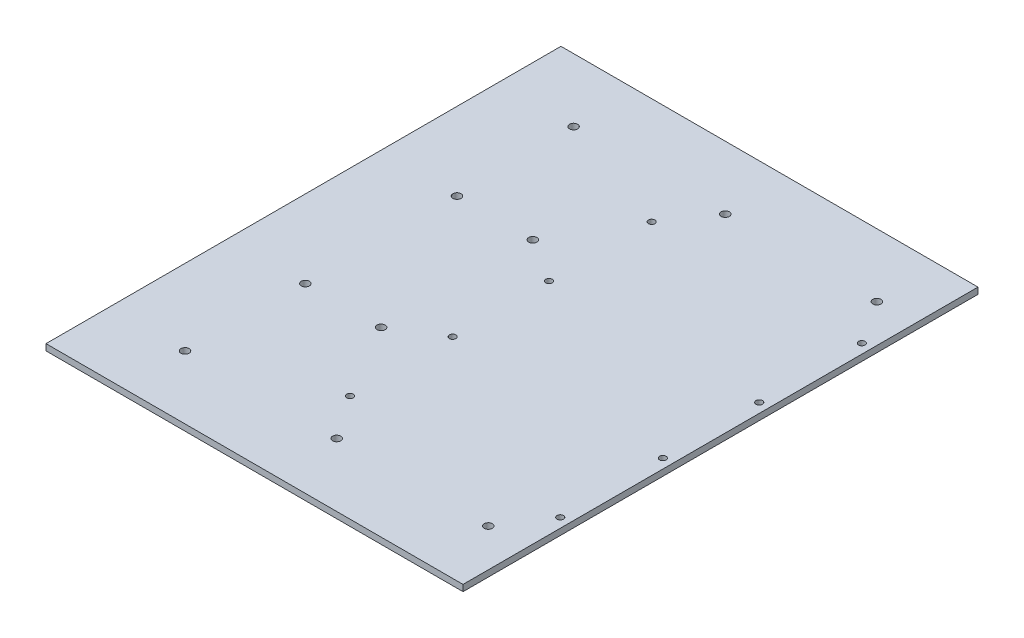
SolidWorks part; units mm, degrees
ref_plane "Front Plane" through (0, 0, 0) normal (0, 0, 1) x (1, 0, 0)
ref_plane "Top Plane" through (0, 0, 0) normal (0, 1, 0) x (1, 0, 0)
ref_plane "Right Plane" through (0, 0, 0) normal (1, 0, 0) x (0, 0, -1)
sketch "Sketch1" plane through (0, 0, 0) normal (0, 1, 0) x (1, 0, 0)
  line L0 (-116.1676, -258.7625) -> (302.9324, 258.7625) construction
  line L1 (-116.1676, -258.7625) -> (302.9324, -258.7625)
  line L2 (-116.1676, -258.7625) -> (-116.1676, 258.7625)
  line L3 (-116.1676, 258.7625) -> (302.9324, 258.7625)
  line L4 (302.9324, -258.7625) -> (302.9324, 258.7625)
  line L5 (-116.1676, 258.7625) -> (302.9324, -258.7625) construction
  point P0 (0, 0)
  point P6 (93.3824, 0)
  point P8 (93.3824, 0)
  dimension "D1" = 517.525
  dimension "D2" = 419.1
extrude "Boss-Extrude1" add sketch "Sketch1" against normal blind 6.35
sketch "Sketch2" plane through (0, 0, 0) normal (0, 1, 0) x (1, 0, 0)
  line L0 (-116.1676, 0) -> (302.9324, 0) construction
  line L1 (-116.1676, 258.7625) -> (-116.1676, -258.7625) construction
  line L2 (302.9324, -258.7625) -> (302.9324, 258.7625) construction
  line L3 (82.1429, -258.7625) -> (82.1429, 258.7625) construction
  line L4 (264.8324, -258.7625) -> (264.8324, 258.7625) construction
  line L5 (-116.1676, 195.2625) -> (302.9324, 195.2625) construction
  line L6 (-116.1676, -195.2625) -> (302.9324, -195.2625) construction
  line L7 (293.4074, 258.7625) -> (293.4074, -258.7625) construction
  line L8 (302.9324, 258.7625) -> (-116.1676, 258.7625) construction
  line L9 (25.4, -38.1) -> (-25.4, -38.1)
  line L10 (25.4, -38.1) -> (25.4, 38.1)
  line L11 (25.4, 38.1) -> (-25.4, 38.1)
  line L12 (-25.4, -38.1) -> (-25.4, 38.1)
  line L13 (25.4, -38.1) -> (-25.4, 38.1) construction
  line L14 (25.4, 38.1) -> (-25.4, -38.1) construction
  line L15 (-116.1676, -258.7625) -> (302.9324, -258.7625) construction
  point P12 (0, 0)
  point P14 (293.4074, 48.438)
  point P20 (293.4074, 151.562)
  point P22 (82.1429, 48.438)
  point P23 (82.1429, 151.562)
  point P26 (82.1429, -151.562)
  point P27 (82.1429, -48.438)
  point P28 (293.4074, -151.562)
  point P29 (293.4074, -48.438)
  dimension "D1" = 76.2
  dimension "D2" = 50.8
  dimension "D3" = 9.525
  dimension "D4" = 211.2645
  dimension "D5" = 38.1
  dimension "D6" = 63.5
hole_wizard "F (0.257) Diameter Hole1" positions "Sketch3" profile "Sketch4" hole size "F" standard "ANSI Inch" end condition up to next
sketch "Sketch3" plane through (0, 0, 0) normal (0, 1, 0) x (1, 0, 0)
  point P0 (82.1429, -151.562)
  point P3 (293.4074, -151.562)
  point P6 (82.1429, -48.438)
  point P9 (293.4074, -48.438)
  point P12 (293.4074, 48.438)
  point P15 (82.1429, 48.438)
  point P18 (82.1429, 151.562)
  point P21 (293.4074, 151.562)
sketch "Sketch4" plane through (82.1429, 0, 151.562) normal (1, 0, 0) x (0, 0, 1)
  line L0 (0, 0) -> (0, 6.35)
  line L1 (0, 6.35) -> (3.2639, 6.35)
  line L2 (3.2639, 6.35) -> (3.2639, 0)
  line L5 (3.2639, 0) -> (0, 0)
  line L11 (0, -6.35) -> (0, 107.95) construction
  dimension "Thru Hole Dia." = 6.5278
  dimension "Thru Hole Depth" = 6.35
sketch "Sketch5" plane through (0, 0, 0) normal (0, 1, 0) x (1, 0, 0)
  line L0 (-116.1676, 258.7625) -> (-116.1676, -258.7625) construction
  line L2 (-116.1676, 233.3625) -> (-116.1676, 258.7625)
  line L3 (302.9324, 0) -> (-116.1676, 0) construction
  line L4 (82.1429, 258.7625) -> (-116.1676, 258.7625)
  line L5 (82.1429, 233.3625) -> (-116.1676, 233.3625)
  line L6 (82.1429, 233.3625) -> (82.1429, 258.7625)
  line L7 (82.1429, -233.3625) -> (-116.1676, -233.3625)
  line L8 (82.1429, -233.3625) -> (82.1429, -258.7625)
  line L9 (82.1429, -258.7625) -> (-116.1676, -258.7625)
  line L10 (-116.1676, -233.3625) -> (-116.1676, -258.7625)
  dimension "D3" = 25.4
  dimension "D4" = 198.3105
extrude "Cut-Extrude1" [suppressed] cut sketch "Sketch5" against normal through all
sketch "Sketch6" plane through (0, 0, 0) normal (0, 1, 0) x (1, 0, 0)
  line L1 (38.1, -76.2) -> (-38.1, -76.2)
  line L2 (38.1, -76.2) -> (38.1, 76.2)
  line L3 (38.1, 76.2) -> (-38.1, 76.2)
  line L4 (-38.1, -76.2) -> (-38.1, 76.2)
  line L5 (38.1, -76.2) -> (-38.1, 76.2) construction
  line L6 (38.1, 76.2) -> (-38.1, -76.2) construction
  point P0 (0, 0)
  dimension "D1" = 76.2
  dimension "D2" = 152.4
hole_wizard "P (0.323) Diameter Hole1" positions "Sketch7" profile "Sketch8" hole size "P" standard "ANSI Inch" end condition through all
sketch "Sketch7" plane through (0, 0, 0) normal (0, 1, 0) x (1, 0, 0)
  point P0 (-38.1, -76.2)
  point P3 (38.1, -76.2)
  point P6 (38.1, 76.2)
  point P9 (-38.1, 76.2)
sketch "Sketch8" plane through (-38.1, 0, 76.2) normal (1, 0, 0) x (0, 0, 1)
  line L0 (0, 0) -> (0, 6.35)
  line L1 (0, 6.35) -> (4.1021, 6.35)
  line L2 (4.1021, 6.35) -> (4.1021, 0)
  line L5 (4.1021, 0) -> (0, 0)
  line L11 (0, -6.35) -> (0, 107.95) construction
  dimension "Thru Hole Dia." = 8.2042
  dimension "Thru Hole Depth" = 6.35
sketch "Sketch9" plane through (0, 0, 0) normal (0, 1, 0) x (1, 0, 0)
  line L0 (302.9324, -258.7625) -> (302.9324, 258.7625) construction
  line L2 (-116.1676, -258.7625) -> (302.9324, -258.7625) construction
  circle A0 centre (264.8324, -195.2625) radius 4.1021
  circle A1 centre (112.4324, -195.2625) radius 4.1021
  circle A2 centre (-39.9676, -195.2625) radius 4.1021
  circle A3 centre (112.4324, 195.2625) radius 4.1021
  circle A4 centre (-39.9676, 195.2625) radius 4.1021
  circle A5 centre (264.8324, 195.2625) radius 4.1021
  dimension "D1" = 8.2042
  dimension "D2" = 38.1
  dimension "D3" = 63.5
  dimension "D4" = 3
  dimension "D5" = 2
extrude "Cut-Extrude2" cut sketch "Sketch9" against normal up to next
